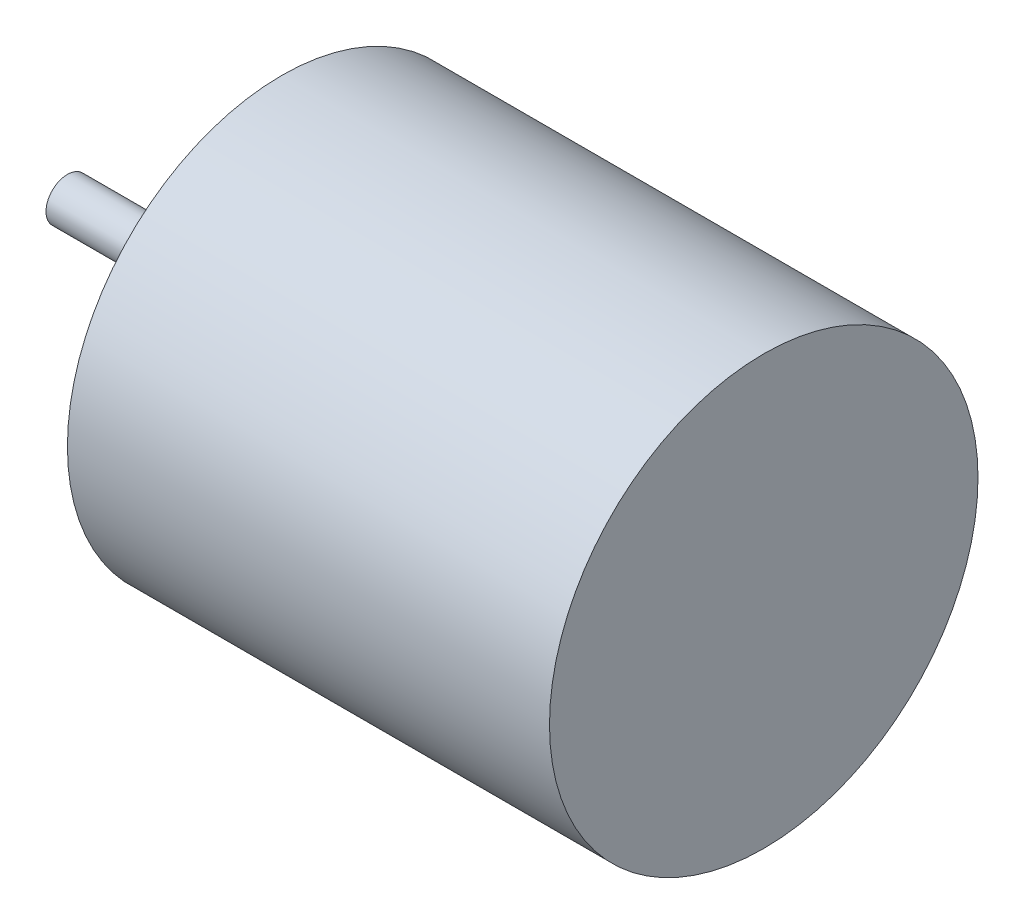
SolidWorks part; units mm, degrees
ref_plane "Front" through (0, 0, 0) normal (0, 0, 1) x (1, 0, 0)
ref_plane "Top" through (0, 0, 0) normal (0, 1, 0) x (1, 0, 0)
ref_plane "Right" through (0, 0, 0) normal (1, 0, 0) x (0, 0, -1)
sketch "Sketch1" plane through (0, 0, 0) normal (0, 0, 1) x (1, 0, 0)
  line L0 (0, 0) -> (0, 4)
  line L1 (0, 4) -> (9, 4)
  line L2 (9, 4) -> (9, 0)
  line L3 (9, 0) -> (0, 0)
  line L4 (0, 0) -> (-4, 0)
  line L5 (-4, 0) -> (-4, 0.4)
  line L6 (-4, 0.4) -> (0, 0.4)
  dimension "D1" = 4
  dimension "D2" = 0.4
  dimension "D3" = 9
  dimension "D4" = 4
revolve "Revolve1" add sketch "Sketch1" angle 360 about L3
